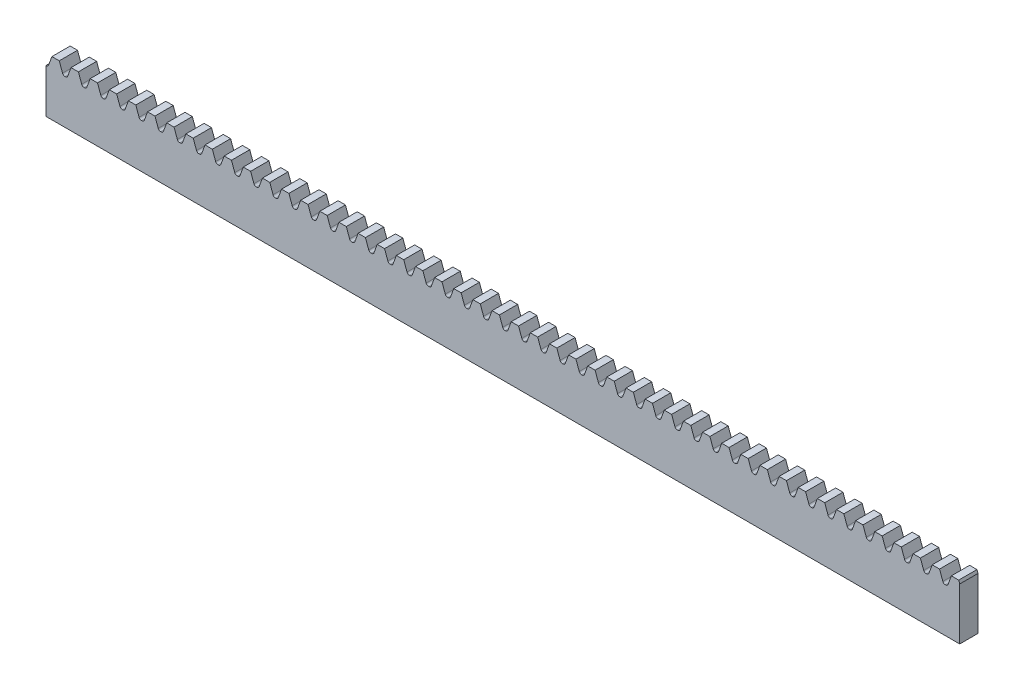
SolidWorks part; units mm, degrees
material "MC Nylon"
ref_plane "Front Plane" through (0, 0, 0) normal (0, 0, 1) x (1, 0, 0)
ref_plane "Top Plane" through (0, 0, 0) normal (0, 1, 0) x (1, 0, 0)
ref_plane "Right Plane" through (0, 0, 0) normal (1, 0, 0) x (0, 0, -1)
sketch "Sketch1" plane through (0, 0, 0) normal (0, 0, 1) x (1, 0, 0)
  line L1 (0, 0) -> (150, 0)
  line L2 (0, 0) -> (0, 9)
  line L3 (0, 9) -> (150, 9)
  line L4 (150, 0) -> (150, 9)
  dimension "L" = 150
  dimension "H" = 9
extrude "Boss-Extrude1" add sketch "Sketch1" against normal mid plane 3
sketch "Sketch2" plane through (0, 0, 1.5) normal (0, 0, 1) x (1, 0, 0)
  line L0 (0, 0) -> (0, 9) construction
  line L2 (-0.9674, 9) -> (0.9674, 9)
  line L3 (0.9674, 9) -> (0.4262, 7.5132)
  line L4 (0.0504, 7.25) -> (-0.0504, 7.25)
  line L5 (150, 0) -> (150, 9) construction
  line L6 (-0.7854, 8.5) -> (150, 8.5) construction
  line L9 (-0.9674, 9) -> (-0.4262, 7.5132)
  line L10 (0, 9) -> (0, 0) construction
  line L11 (150, 9) -> (0, 9) construction
  arc A0 (0.4262, 7.5132) -> (0.0504, 7.25) centre (0.0504, 7.65) cw
  arc A1 (-0.4262, 7.5132) -> (-0.0504, 7.25) centre (-0.0504, 7.65) ccw
  dimension "D3" = 0.4
  dimension "H_s" = 8.5
  dimension "D2" = 20
extrude "Cut-Extrude1" cut sketch "Sketch2" against normal through all
pattern_linear "LPattern1" count 49 spacing 3.1416 along (1, 0, 0) of "Cut-Extrude1"
hole_wizard "Tapped Hole1" [suppressed] positions "Sketch4" profile "Sketch3" tap size "M3x0.5" standard "JIS"
sketch "Sketch4" [suppressed] plane through (0, 0, 0) normal (-1, 0, 0) x (0, 0, 1)
  line L2 (-5, 0) -> (5, 0) construction
  point P0 (0, 5.5)
sketch "Sketch3" [suppressed] plane through (0, 5.5, 0) normal (0, 1, 0) x (0, 0, 1)
  line L0 (0, 0) -> (0, 8.2511)
  line L1 (0, 8.2511) -> (1.25, 7.5)
  line L2 (1.25, 7.5) -> (1.25, 0)
  line L5 (1.25, 0) -> (0, 0)
  line L10 (0, 8.2511) -> (-1.25, 7.5) construction
  line L11 (0, 0) -> (0, 8.2511) construction
  dimension "Tap Drill Dia." = 2.5
  dimension "Tap Drill Depth" = 7.5
  dimension "Drill Angle" = 118
cosmetic thread "Hole Thread1" [suppressed] parameters "MCx2"=6, "MC"=3
hole_wizard "Tapped Hole2" [suppressed] positions "Sketch6" profile "Sketch5" tap size "M3x0.5" standard "JIS"
sketch "Sketch6" [suppressed] plane through (0, 0, 0) normal (-1, 0, 0) x (0, 0, 1)
  line L1 (-5, 0) -> (5, 0) construction
  line L3 (0, 0) -> (0, 12) construction
  line L5 (-5, 12) -> (5, 12) construction
  point P0 (0, 5.5)
sketch "Sketch5" [suppressed] plane through (0, 5.5, 0) normal (0, 1, 0) x (0, 0, 1)
  line L0 (0, 0) -> (0, 8.2511)
  line L1 (0, 8.2511) -> (1.25, 7.5)
  line L2 (1.25, 7.5) -> (1.25, 0)
  line L5 (1.25, 0) -> (0, 0)
  line L10 (0, 8.2511) -> (-1.25, 7.5) construction
  line L11 (0, 0) -> (0, 8.2511) construction
  dimension "Tap Drill Dia." = 2.5
  dimension "Tap Drill Depth" = 7.5
  dimension "Drill Angle" = 118
cosmetic thread "Hole Thread2" [suppressed] parameters "WMCx2"=6, "WMC"=3
hole_wizard "Tapped Hole3" [suppressed] positions "Sketch8" profile "Sketch7" tap size "M3x0.5" standard "JIS"
sketch "Sketch8" [suppressed] plane through (100, -0.0905, -0.628) normal (1, 0, 0) x (0, 0, -1)
  point P0 (-0.628, 5.5905)
sketch "Sketch7" [suppressed] plane through (100, 5.5, 0) normal (0, 1, 0) x (0, 0, -1)
  line L0 (0, 0) -> (0, 8.2511)
  line L1 (0, 8.2511) -> (1.25, 7.5)
  line L2 (1.25, 7.5) -> (1.25, 0)
  line L5 (1.25, 0) -> (0, 0)
  line L10 (0, 8.2511) -> (-1.25, 7.5) construction
  line L11 (0, 0) -> (0, 8.2511) construction
  dimension "Tap Drill Dia." = 2.5
  dimension "Tap Drill Depth" = 7.5
  dimension "Drill Angle" = 118
cosmetic thread "Hole Thread3" [suppressed] parameters "WMCx2"=6, "WMC"=3
equation "\"Module\"= 1.0"
equation "\"D1@LPattern1\"=int ( ( \"L@Sketch1\" / ( \"Module\" * PI ) ) ) + 2"
equation "\"P@LPattern1\"=\"Module\"*PI"
equation "\"D1@Sketch2\"=1.25*\"Module\""
equation "\"D3@Sketch2\"=0.4*\"Module\""
equation "\"D4@Sketch2\"=(\"Module\"*PI)/2"
equation "\"D1@Sketch4\" = \"H_s@Sketch2\" / 2"
equation "\"D1@Sketch6\"=\"H_s@Sketch2\"/2"
